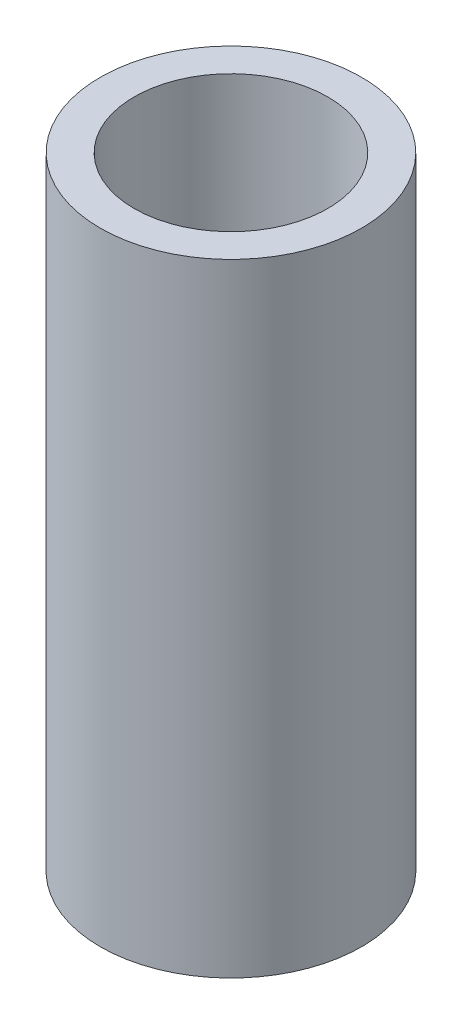
SolidWorks part; units mm, degrees
ref_plane "Front Plane" through (0, 0, 0) normal (0, 0, 1) x (1, 0, 0)
ref_plane "Top Plane" through (0, 0, 0) normal (0, 1, 0) x (1, 0, 0)
ref_plane "Right Plane" through (0, 0, 0) normal (1, 0, 0) x (0, 0, -1)
sketch "Sketch1" plane through (0, 0, 0) normal (0, 1, 0) x (1, 0, 0)
  circle A0 centre (0, 0) radius 7.8994
  circle A1 centre (0, 0) radius 10.668
  dimension "D1" = 21.336
  dimension "D2" = 15.7988
extrude "Boss-Extrude1" add sketch "Sketch1" along normal blind 50.8
